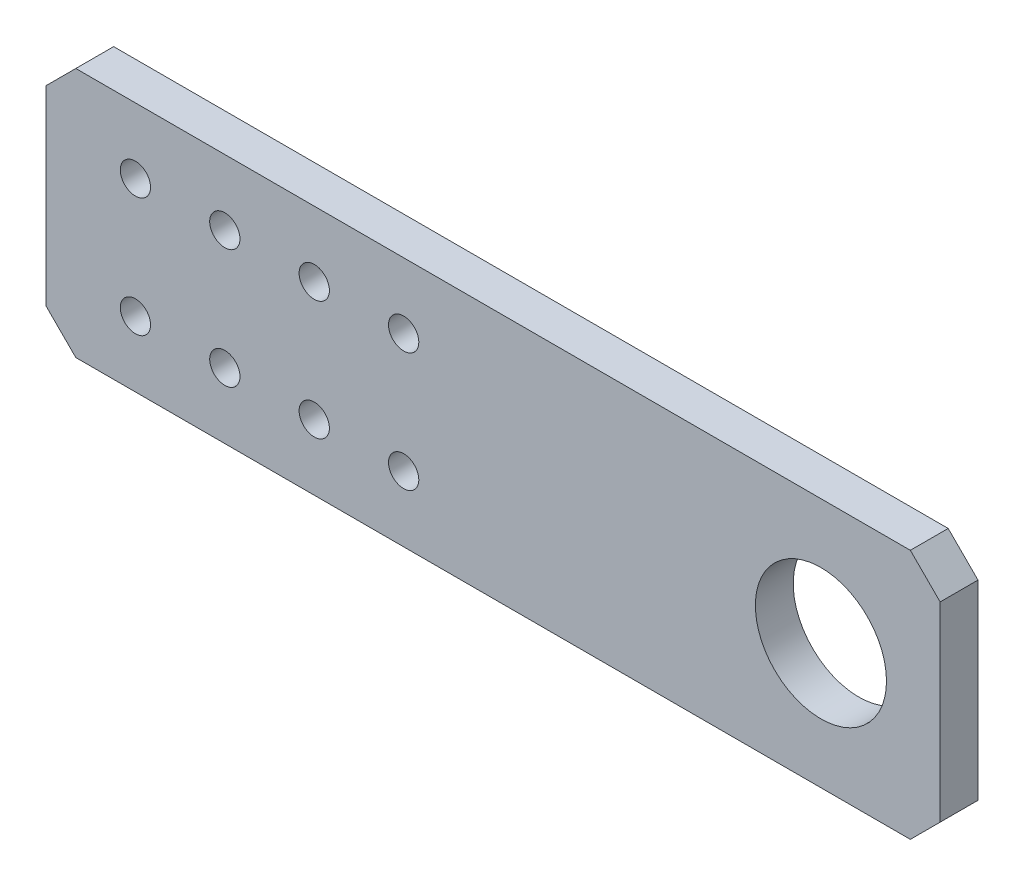
SolidWorks part; units mm, degrees
ref_plane "Front Plane" through (0, 0, 0) normal (0, 0, 1) x (1, 0, 0)
ref_plane "Top Plane" through (0, 0, 0) normal (0, 1, 0) x (1, 0, 0)
ref_plane "Right Plane" through (0, 0, 0) normal (1, 0, 0) x (0, 0, -1)
sketch "Sketch1" plane through (0, 0, 0) normal (0, 0, 1) x (1, 0, 0)
  line L1 (-100, 21) -> (100, 21)
  line L2 (-100, 21) -> (-100, -21)
  line L3 (-100, -21) -> (100, -21)
  line L4 (100, 21) -> (100, -21)
  line L5 (-100, 21) -> (100, -21) construction
  line L6 (-100, -21) -> (100, 21) construction
  point P0 (0, 0)
  dimension "D1" = 200
  dimension "D2" = 42
extrude "Boss-Extrude1" add sketch "Sketch1" along normal blind 6.35
sketch "Sketch3" plane through (0, 0, 6.35) normal (0, 0, 1) x (1, 0, 0)
  line L0 (-60, 10) -> (-60, -10) construction
  line L1 (-100, 21) -> (-100, -21) construction
  circle A0 centre (-60, 10) radius 2
  circle A1 centre (-60, -10) radius 2
  point P4 (-60, 0)
  dimension "D1" = 4
  dimension "D2" = 20
  dimension "D3" = 40
sketch "Sketch4" plane through (0, 0, 6.35) normal (0, 0, 1) x (1, 0, 0)
  line L0 (-100, 21) -> (-100, -21) construction
  line L1 (100, -21) -> (100, 21) construction
  circle A0 centre (-76, 0) radius 2.286
  circle A1 centre (80, 0) radius 2.286 construction
  dimension "D2" = 4.572
  dimension "D3" = 20
  dimension "D1" = 24
  dimension "D4" = 156
extrude "Cut-Extrude3" cut sketch "Sketch4" against normal through all
chamfer "Chamfer1" distance 5 angle 45 4 edges at (-100, 21, 3.175) (-100, -21, 3.175) (100, 21, 3.175) (100, -21, 3.175)
sketch "Sketch5" [suppressed] plane through (0, 0, 6.35) normal (0, 0, 1) x (1, 0, 0)
  line L0 (100, -16) -> (100, 16) construction
  circle A0 centre (77, 0) radius 11
  dimension "D1" = 22
  dimension "D2" = 23
extrude "Cut-Extrude4" [suppressed] cut sketch "Sketch5" against normal blind 25
sketch "Sketch8" plane through (0, 0, 6.35) normal (0, 0, 1) x (1, 0, 0)
  line L4 (25.5, 3.175) -> (10.5, 3.175)
  line L5 (10.5, 3.175) -> (10.5, -3.175)
  line L6 (10.5, -3.175) -> (25.5, -3.175)
  line L7 (25.5, -3.175) -> (25.5, 3.175)
  line L8 (25.5, 3.175) -> (10.5, 3.175)
  line L9 (10.5, 3.175) -> (10.5, -3.175)
  line L10 (10.5, -3.175) -> (25.5, -3.175)
  line L11 (25.5, -3.175) -> (25.5, 3.175)
  dimension "D1" = 0
extrude "Cut-Extrude7" [suppressed] cut sketch "Sketch8" against normal through all
sketch "Sketch9" plane through (0, 0, 6.35) normal (0, 0, 1) x (1, 0, 0)
  circle A1 centre (80, 0) radius 2.286 construction
  circle A2 centre (80, 0) radius 11
  dimension "D1" = 22
extrude "Cut-Extrude8" cut sketch "Sketch9" against normal through all
sketch "Sketch10" [suppressed] plane through (0, 0, 6.35) normal (0, 0, 1) x (1, 0, 0)
  circle A0 centre (80, 0) radius 15
  dimension "D1" = 25
extrude "Cut-Extrude9" [suppressed] cut sketch "Sketch10" against normal through all
sketch "Sketch11" plane through (0, 0, 6.35) normal (0, 0, 1) x (1, 0, 0)
  circle A0 centre (95.5563, 15.5563) radius 1.5 construction
  circle A1 centre (64.4437, 15.5563) radius 1.5 construction
  circle A2 centre (95.5563, -15.5563) radius 1.5 construction
  circle A3 centre (64.4437, -15.5563) radius 1.5 construction
  circle A4 centre (95.5563, 15.5563) radius 1.5
  circle A5 centre (64.4437, 15.5563) radius 1.5
  circle A6 centre (95.5563, -15.5563) radius 1.5
  circle A7 centre (64.4437, -15.5563) radius 1.5
sketch "Sketch12" plane through (0, 0, 6.35) normal (0, 0, 1) x (1, 0, 0)
  line L0 (-100, 16) -> (-100, -16) construction
  circle A0 centre (-93, 0) radius 2.286
  point P4 (-100, 0)
  dimension "D1" = 4.572
  dimension "D2" = 7
extrude "Cut-Extrude11" cut sketch "Sketch12" against normal through all
sketch "Sketch13" plane through (0, 0, 6.35) normal (0, 0, 1) x (1, 0, 0)
  line L0 (-50, 16) -> (-50, -16)
  line L1 (-45, 21) -> (-50, 16)
  line L2 (-50, -16) -> (-45, -21)
  line L3 (-95, -21) -> (95, -21) construction
  line L4 (95, 21) -> (-95, 21) construction
  line L5 (-95, -21) -> (95, -21)
  line L6 (95, 21) -> (-95, 21)
  line L7 (0, 0) -> (-50, 0) construction
  line L8 (95, 21) -> (-95, 21)
  line L9 (-95, 21) -> (-100, 16)
  line L10 (-100, 16) -> (-100, -16)
  line L11 (-100, -16) -> (-95, -21)
  line L12 (-95, -21) -> (95, -21)
  line L13 (95, -21) -> (100, -16)
  line L14 (100, -16) -> (100, 16)
  line L15 (100, 16) -> (95, 21)
  line L16 (95, 21) -> (-45, 21)
  line L17 (-95, 21) -> (-100, 16)
  line L18 (-100, 16) -> (-100, -16)
  line L19 (-100, -16) -> (-95, -21)
  line L20 (-45, -21) -> (95, -21)
  line L21 (95, -21) -> (100, -16)
  line L22 (100, -16) -> (100, 16)
  line L23 (100, 16) -> (95, 21)
  circle A0 centre (-35, 10) radius 2.54
  circle A1 centre (-20, 10) radius 2.54
  circle A2 centre (-5, 10) radius 2.54
  circle A3 centre (10, 10) radius 2.54
  circle A4 centre (-20, -10) radius 2.54
  circle A5 centre (-5, -10) radius 2.54
  circle A6 centre (10, -10) radius 2.54
  circle A7 centre (-35, -10) radius 2.54
  point P2 (-50, 21)
  point P9 (-50, -21)
  circle M9 centre (-93, 0) radius 2.286
  circle M11 centre (-76, 0) radius 2.286
  line M12 (95, 21) -> (-95, 21)
  line M13 (-95, 21) -> (-100, 16)
  line M14 (-100, 16) -> (-100, -16)
  line M15 (-100, -16) -> (-95, -21)
  line M16 (-95, -21) -> (95, -21)
  dimension "D7" = 5.08
  dimension "D2" = 150
  dimension "D3" = 10
  dimension "D4" = 15
  dimension "D1" = 0
  dimension "D8" = 4
  dimension "D9" = 2
extrude "Cut-Extrude12" cut sketch "Sketch13" against normal blind 10 contours L2 L0 L1 M12 M13 M14 M15 M16 M11 M9 | A0 | A7 | A1 | A4 | A2 | A5 | A3 | A6
